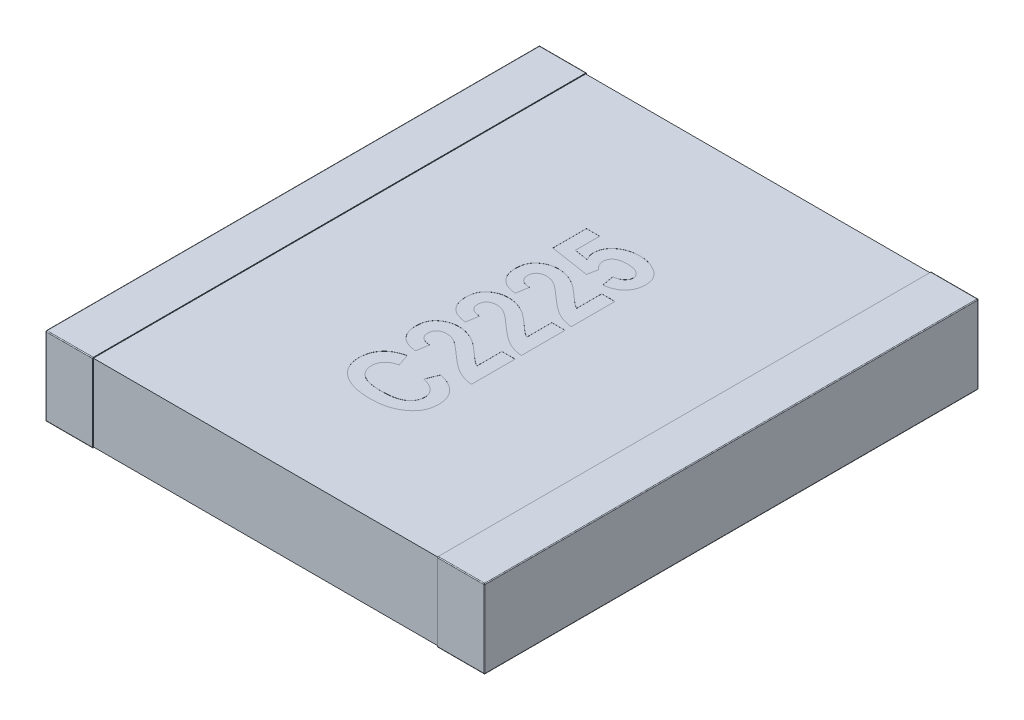
SolidWorks part; units mm, degrees
ref_plane "Front Plane" through (0, 0, 0) normal (0, 0, 1) x (1, 0, 0)
ref_plane "Top Plane" through (0, 0, 0) normal (0, 1, 0) x (1, 0, 0)
ref_plane "Right Plane" through (0, 0, 0) normal (1, 0, 0) x (0, 0, -1)
sketch "Sketch1" plane through (0, 0, 0) normal (0, 1, 0) x (1, 0, 0)
  line L0 (0, 0.15) -> (0, -0.15) construction
  line L1 (-2.8, 0) -> (0, 0) construction
  line L3 (-2.8, 3.15) -> (-2.2, 3.15)
  line L4 (-2.8, 3.15) -> (-2.8, -3.15)
  line L5 (-2.8, -3.15) -> (-2.2, -3.15)
  line L6 (-2.2, 3.15) -> (-2.2, -3.15)
  dimension "BANDWIDTH" = 0.6
  dimension "WIDTH" = 6.3
  dimension "LENGTH-HALF" = 2.8
extrude "THICKNESS" add sketch "Sketch1" along normal blind 1
fillet "Fillet1" radius 0.01 8 edges at (-2.8, 0, 0) (-2.5, 0, -3.15) (-2.8, 0.5, -3.15) (-2.5, 0, 3.15) (-2.8, 0.5, 3.15) (-2.8, 1, 0) (-2.5, 1, -3.15) (-2.5, 1, 3.15)
sketch "Sketch2" plane through (0, 0, 0) normal (1, 0, 0) x (0, 0, -1)
  line L0 (0, 1) -> (0, 0) construction
  line L1 (-3.14, 0.99) -> (3.14, 0.99)
  line L2 (-3.14, 0.99) -> (-3.14, 0.01)
  line L3 (-3.14, 0.01) -> (3.14, 0.01)
  line L4 (3.14, 0.99) -> (3.14, 0.01)
  line L5 (-3.14, 1) -> (3.14, 1) construction
  line L6 (-3.14, 0) -> (3.14, 0) construction
  line L7 (-3.15, 0.5) -> (3.15, 0.5) construction
  line L8 (-3.15, 0.99) -> (-3.15, 0.01) construction
  line L9 (3.15, 0.99) -> (3.15, 0.01) construction
  dimension "D1" = 0.01
  dimension "D2" = 0.01
extrude "Boss-Extrude2" add sketch "Sketch2" against normal up to surface (2.2 mm away) up to face at (-2.2, 0.5, 0)
mirror "Mirror3" about plane through (0, 0, 0) normal (1, 0, 0) of "Boss-Extrude2", "Fillet1", "THICKNESS"
sketch "Sketch3" plane through (0, 0.99, 0) normal (0, 1, 0) x (1, 0, 0)
  line L0 (0.5, -1.875) -> (0.5, 1.875) construction
  line L1 (-0.55, 0) -> (0.55, 0) construction
  line L2 (0, -0.55) -> (0, 0.55) construction
  text T0 "<b>C2225</b>" font "Arial Narrow" height 1
  point P2 (0.5, 0)
  dimension "D1" = 3.75
  dimension "D2" = 0.5
extrude "Cut-Extrude1" cut sketch "Sketch3" against normal blind 0.001
